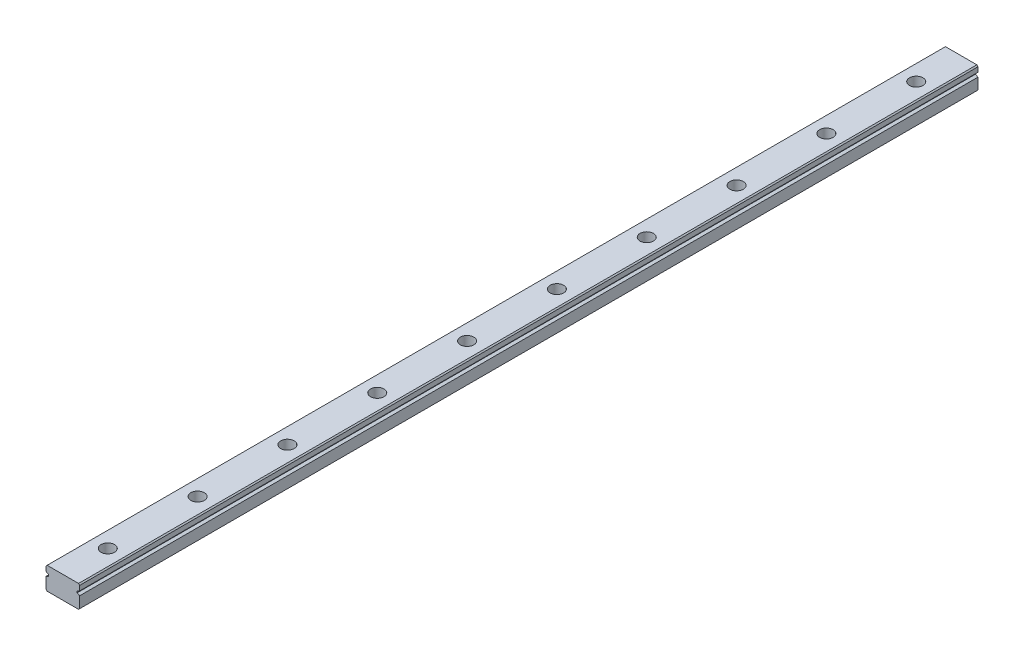
SolidWorks part; units mm, degrees
ref_plane "前视基准面" through (0, 0, 0) normal (0, 0, 1) x (1, 0, 0)
ref_plane "上视基准面" through (0, 0, 0) normal (0, 1, 0) x (1, 0, 0)
ref_plane "右视基准面" through (0, 0, 0) normal (1, 0, 0) x (0, 0, -1)
sketch "草图1" plane through (0, 0, 0) normal (0, 0, 1) x (1, 0, 0)
  line L1 (-3.269, 4.9492) -> (10.731, 4.9492)
  line L2 (-3.769, 4.4492) -> (-3.769, 2.3175)
  line L3 (-3.269, -5.0508) -> (10.731, -5.0508)
  line L4 (11.231, 4.4492) -> (11.231, 2.3175)
  line L6 (11.231, 0.4492) -> (10.0868, 0.9834)
  line L7 (10.0868, 0.9834) -> (10.0868, 1.7834)
  line L8 (-3.769, 0.4492) -> (-2.6248, 0.9834)
  line L9 (11.231, 2.3175) -> (10.0868, 1.7834)
  line L10 (-2.6248, 0.9834) -> (-2.6248, 1.7834)
  line L11 (-3.769, 2.3175) -> (-2.6248, 1.7834)
  line L12 (-3.769, 0.4492) -> (-3.769, -4.5508)
  line L13 (11.231, 0.4492) -> (11.231, -4.5508)
  line L14 (-3.769, 4.4492) -> (-3.269, 4.9492)
  line L15 (10.731, 4.9492) -> (11.231, 4.4492)
  line L16 (11.231, -4.5508) -> (10.731, -5.0508)
  line L17 (-3.769, -4.5508) -> (-3.269, -5.0508)
  point P0 (-3.769, 4.9492)
  point P1 (11.231, -5.0508)
  point P2 (-3.769, -5.0508)
  point P3 (11.231, 4.9492)
  point P15 (10.0868, 1.3834)
  dimension "D1" = 15
  dimension "D2" = 10
extrude "凸台-拉伸1" add sketch "草图1" against normal blind 400
ref_plane "基准面4" through (10.731, 4.9492, 0) normal (0, 0, 1) x (1, 0, 0)
sketch "草图3" plane through (0, 4.9492, 0) normal (0, 1, 0) x (1, 0, 0)
  line L0 (3.731, 400) -> (3.731, 0)
  line L1 (10.731, 400) -> (-3.269, 400) construction
  line L2 (10.731, 0) -> (-3.269, 0) construction
  line L3 (3.731, 200) -> (60.7851, 200)
  line L4 (24.4685, 180) -> (-12.5662, 180)
  line L5 (24.4685, 140) -> (-12.5662, 140)
  line L6 (24.4685, 100) -> (-12.5662, 100)
  line L7 (24.4685, 60) -> (-12.5662, 60)
  line L8 (24.4685, 20) -> (-12.5662, 20)
  line L9 (24.4685, 380) -> (-12.5662, 380)
  line L10 (24.4685, 340) -> (-12.5662, 340)
  line L11 (24.4685, 300) -> (-12.5662, 300)
  line L12 (24.4685, 260) -> (-12.5662, 260)
  line L13 (24.4685, 220) -> (-12.5662, 220)
  dimension "D1" = 20
  dimension "D2" = 40
  dimension "D3" = 40
  dimension "D4" = 40
  dimension "D5" = 40
hole_wizard "孔2" positions "3D草图3" profile "草图7" legacy end condition through all
sketch3d "3D草图3"
  line L0 (3.731, 4.9492, -400) -> (3.731, 4.9492, 0) construction
  line L1 (24.4685, 4.9492, -380) -> (-12.5662, 4.9492, -380) construction
  line L2 (24.4685, 4.9492, -340) -> (-12.5662, 4.9492, -340) construction
  line L3 (24.4685, 4.9492, -300) -> (-12.5662, 4.9492, -300) construction
  line L4 (24.4685, 4.9492, -260) -> (-12.5662, 4.9492, -260) construction
  line L5 (24.4685, 4.9492, -220) -> (-12.5662, 4.9492, -220) construction
  line L6 (24.4685, 4.9492, -180) -> (-12.5662, 4.9492, -180) construction
  line L7 (24.4685, 4.9492, -140) -> (-12.5662, 4.9492, -140) construction
  line L8 (24.4685, 4.9492, -100) -> (-12.5662, 4.9492, -100) construction
  line L9 (24.4685, 4.9492, -60) -> (-12.5662, 4.9492, -60) construction
  line L10 (24.4685, 4.9492, -20) -> (-12.5662, 4.9492, -20) construction
  point P0 (3.731, 4.9492, -380)
  point P6 (3.731, 4.9492, -340)
  point P10 (3.731, 4.9492, -300)
  point P14 (3.731, 4.9492, -260)
  point P18 (3.731, 4.9492, -220)
  point P22 (3.731, 4.9492, -180)
  point P26 (3.731, 4.9492, -140)
  point P30 (3.731, 4.9492, -100)
  point P34 (3.731, 4.9492, -60)
  point P38 (3.731, 4.9492, -20)
sketch "草图7" plane through (3.731, 4.9492, -380) normal (1, 0, 0) x (0, 0, 1)
  line L0 (0, 0) -> (0, 10)
  line L1 (0, 10) -> (1.6, 10)
  line L2 (1.6, 10) -> (1.6, 4.5)
  line L3 (1.6, 4.5) -> (3, 4.5)
  line L4 (3, 4.5) -> (3, 0)
  line L5 (3, 0) -> (0, 0)
  line L6 (0, 110) -> (0, -10) construction
  dimension "直径" = 3.2
  dimension "深度" = 10
  dimension "柱坑直径" = 6
  dimension "柱坑深度" = 4.5
